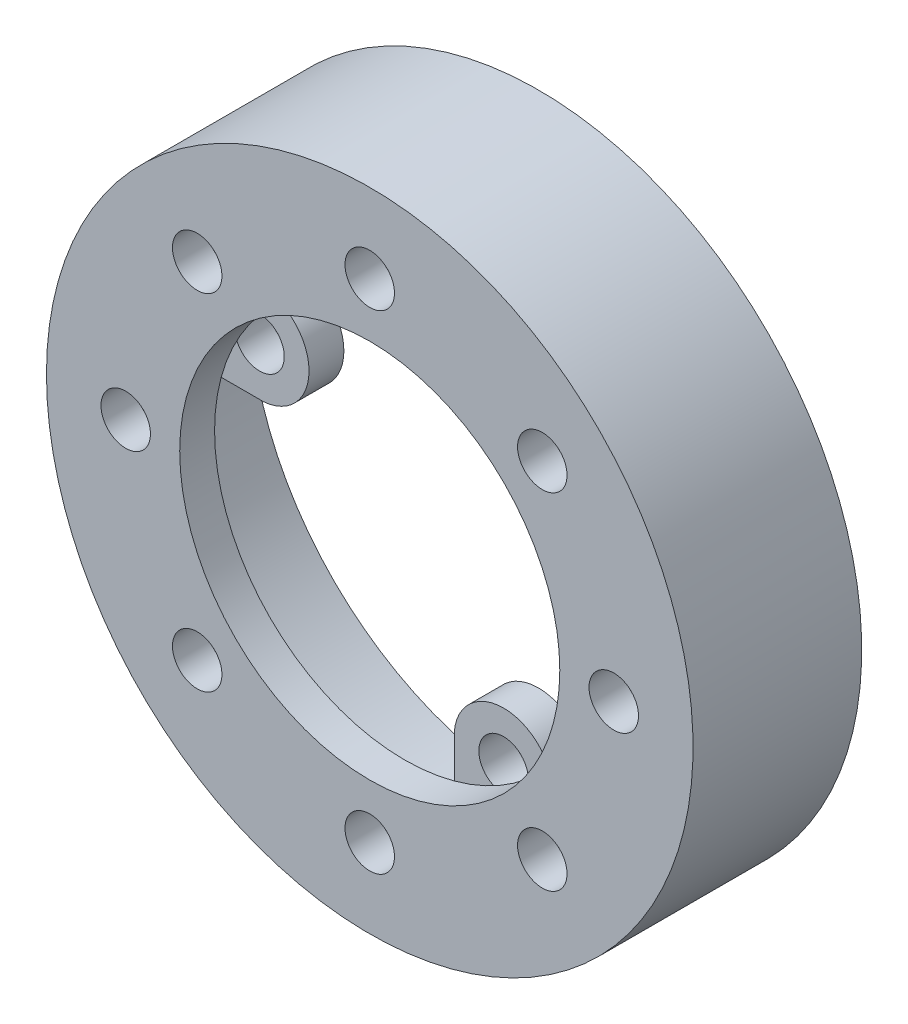
SolidWorks part; units mm, degrees
ref_plane "Front Plane" through (0, 0, 0) normal (0, 0, 1) x (1, 0, 0)
ref_plane "Top Plane" through (0, 0, 0) normal (0, 1, 0) x (1, 0, 0)
ref_plane "Right Plane" through (0, 0, 0) normal (1, 0, 0) x (0, 0, -1)
sketch "Sketch1" plane through (0, 0, 0) normal (0, 1, 0) x (1, 0, 0)
  line L0 (73.025, 0) -> (73.025, 7.874)
  line L1 (42.926, 0) -> (73.025, 0)
  line L2 (42.926, 0) -> (42.926, 7.874)
  line L3 (42.926, 7.874) -> (65.278, 7.874)
  line L4 (73.025, 7.874) -> (73.025, 38.1)
  line L10 (65.278, 38.1) -> (73.025, 38.1)
  line L11 (65.278, 7.874) -> (65.278, 38.1)
  line L12 (0, 38.1) -> (0, -40.9077) construction
  dimension "D1" = 42.926
  dimension "D2" = 30.099
  dimension "D3" = 7.874
  dimension "D4" = 22.352
  dimension "D5" = 30.226
revolve "Revolve1" add sketch "Sketch1" angle 360 about L12
sketch "Sketch2" plane through (0, 0, -7.874) normal (0, 0, -1) x (-1, 0, 0)
  circle A1 centre (0, 55.118) radius 5.588
  circle A2 centre (0, 0) radius 55.118
  circle A3 centre (0, 0) radius 55.118 construction
  circle A4 centre (38.9743, 38.9743) radius 5.588
  circle A5 centre (55.118, 0) radius 5.588
  circle A6 centre (38.9743, -38.9743) radius 5.588
  circle A7 centre (0, -55.118) radius 5.588
  circle A8 centre (-38.9743, -38.9743) radius 5.588
  circle A9 centre (-55.118, 0) radius 5.588
  circle A10 centre (-38.9743, 38.9743) radius 5.588
  point P22 (0, 0)
  dimension "D2" = 11.176
  dimension "D1" = 10.16
  dimension "D3" = 8
extrude "Cut-Extrude1" cut sketch "Sketch2" against normal through all
sketch "Sketch3" plane through (0, 0, -38.1) normal (0, 0, -1) x (-1, 0, 0)
  line L0 (0, 55.118) -> (0, 43.942) construction
  line L5 (0, 65.278) -> (0, 55.118) construction
  line L6 (11.135, 54.1613) -> (11.135, 64.3213)
  line L7 (-11.135, 54.1613) -> (-11.135, 64.3213)
  line L8 (54.1613, 11.135) -> (64.3213, 11.135)
  line L9 (54.1613, -11.135) -> (64.3213, -11.135)
  line L10 (11.135, -54.1613) -> (11.135, -64.3213)
  line L11 (-11.135, -54.1613) -> (-11.135, -64.3213)
  line L12 (-54.1613, -11.135) -> (-64.3213, -11.135)
  line L13 (-54.1613, 11.135) -> (-64.3213, 11.135)
  circle A0 centre (0, 0) radius 65.278 construction
  circle A1 centre (0, 0) radius 65.278 construction
  circle A2 centre (0, 55.118) radius 5.588
  arc A5 (11.135, 54.1613) -> (-11.135, 54.1613) centre (0, 55.118) cw
  arc A6 (11.135, 64.3213) -> (-11.135, 64.3213) centre (0, 0) ccw
  arc A7 (54.1613, -11.135) -> (54.1613, 11.135) centre (55.118, 0) cw
  arc A8 (64.3213, -11.135) -> (64.3213, 11.135) centre (0, 0) ccw
  circle A9 centre (55.118, 0) radius 5.588
  arc A10 (-11.135, -54.1613) -> (11.135, -54.1613) centre (0, -55.118) cw
  arc A11 (-11.135, -64.3213) -> (11.135, -64.3213) centre (0, 0) ccw
  circle A12 centre (0, -55.118) radius 5.588
  arc A13 (-54.1613, 11.135) -> (-54.1613, -11.135) centre (-55.118, 0) cw
  arc A14 (-64.3213, 11.135) -> (-64.3213, -11.135) centre (0, 0) ccw
  circle A15 centre (-55.118, 0) radius 5.588
  point P36 (0, 0)
  dimension "D3" = 10.16
  dimension "D1" = 11.176
  dimension "D5" = 11.176
  dimension "D2" = 11.176
  dimension "D4" = 4
sketch "Sketch4" plane through (0, 0, 0) normal (0, 1, 0) x (1, 0, 0)
  line L0 (0, 70.6077) -> (0, -44.5142) construction
sketch "Sketch5" plane through (0, 0, -38.1) normal (0, 0, -1) x (-1, 0, 0)
extrude "Boss-Extrude2" add sketch "Sketch3" against normal blind 7.874
